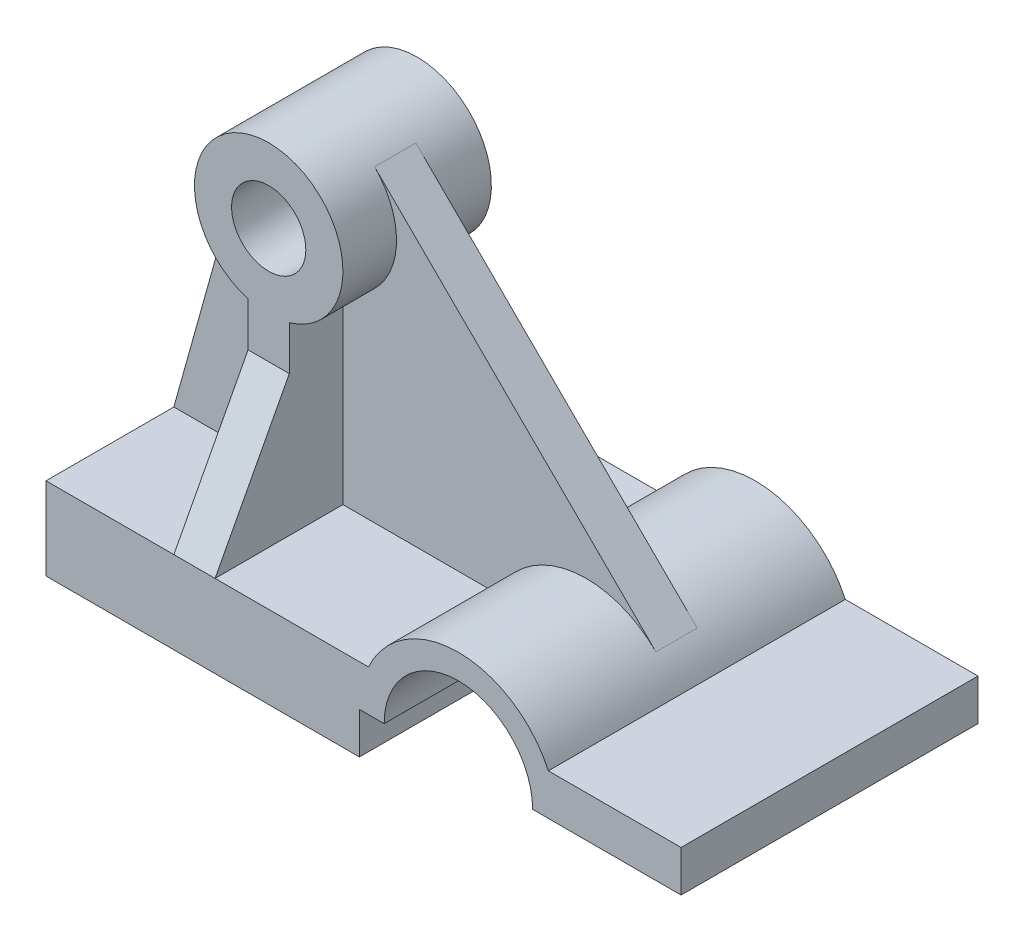
SolidWorks part; units mm, degrees
ref_plane "Front Plane" through (0, 0, 0) normal (0, 0, 1) x (1, 0, 0)
ref_plane "Top Plane" through (0, 0, 0) normal (0, 1, 0) x (1, 0, 0)
ref_plane "Right Plane" through (0, 0, 0) normal (1, 0, 0) x (0, 0, -1)
sketch "Sketch1" plane through (0, 0, 0) normal (0, 0, 1) x (1, 0, 0)
  line L0 (-41.1897, -1.8135) -> (34.8103, -1.8135)
  line L1 (34.8103, -1.8135) -> (34.8103, 8.1865)
  line L2 (34.8103, 8.1865) -> (40.8103, 8.1865)
  line L3 (76.8103, 8.1865) -> (112.8103, 8.1865)
  line L5 (112.8103, 18.1865) -> (80.6277, 18.1865)
  line L6 (36.9929, 18.1865) -> (-41.1897, 18.1865)
  line L7 (-41.1897, 18.1865) -> (-41.1897, -1.8135)
  line L8 (112.8103, 8.1865) -> (112.8103, 18.1865)
  arc A0 (40.8103, 8.1865) -> (76.8103, 8.1865) centre (58.8103, 8.1865) cw
  arc A2 (80.6277, 18.1865) -> (36.9929, 18.1865) centre (58.8103, 8.1865) ccw
  dimension "D3" = 48
  dimension "D6" = 18
  dimension "D1" = 76
  dimension "D2" = 20
  dimension "D4" = 6
  dimension "D5" = 10
  dimension "D7" = 54
extrude "Boss-Extrude1" add sketch "Sketch1" against normal blind 72
sketch "Sketch2" plane through (0, 18.1865, 0) normal (0, 1, 0) x (1, 0, 0)
  line L0 (-41.1897, 72) -> (-41.1897, 0) construction
  line L1 (-23.1897, 54) -> (12.8103, 54)
  line L2 (-23.1897, 54) -> (-23.1897, 18)
  line L3 (-23.1897, 18) -> (12.8103, 18)
  line L4 (12.8103, 54) -> (12.8103, 18)
  line L5 (-23.1897, 54) -> (12.8103, 18) construction
  line L6 (-23.1897, 18) -> (12.8103, 54) construction
  line L8 (36.9929, 0) -> (-41.1897, 0) construction
  point P0 (-5.1897, 36)
  point P9 (-13.1546, 0)
  point P10 (-31.1416, 34.8758)
  dimension "D1" = 36
  dimension "D2" = 36
  dimension "D3" = 36
  dimension "D4" = 36
extrude "Boss-Extrude3" add sketch "Sketch2" along normal blind 80
sketch "Sketch4" plane through (0, 0, -18) normal (0, 0, 1) x (1, 0, 0)
  line L0 (-23.1897, 18.1865) -> (12.8103, 18.1865) construction
  line L1 (12.8103, 98.1865) -> (12.8103, 18.1865) construction
  line L2 (-23.1897, 80.1865) -> (-23.1897, 98.1865)
  line L3 (-23.1897, 98.1865) -> (12.8103, 98.1865)
  line L4 (12.8103, 98.1865) -> (12.8103, 80.1865)
  line L5 (12.8103, 98.1865) -> (12.8103, 80.1865)
  circle A0 centre (-5.1897, 80.1865) radius 18
  circle A1 centre (-5.1897, 80.1865) radius 9
  dimension "D2" = 36
  dimension "D3" = 18
  dimension "D1" = 62
  dimension "D4" = 18
extrude "Cut-Extrude2" cut sketch "Sketch4" against normal blind 80 contours A1
sketch "Sketch5" plane through (0, 0, -18) normal (0, 0, 1) x (1, 0, 0)
  line L0 (-5.1897, 62.1865) -> (-5.1897, 18.1865) construction
  line L1 (-23.1897, 18.1865) -> (12.8103, 18.1865) construction
  line L2 (-10.1897, 62.1865) -> (-10.1897, 18.1865)
  line L3 (-0.1897, 62.1865) -> (-0.1897, 18.1865)
  line L4 (-10.1897, 18.1865) -> (-0.1897, 18.1865)
  line L5 (-23.1897, 80.1865) -> (-23.1897, 98.1865)
  line L6 (-23.1897, 98.1865) -> (12.8103, 98.1865)
  line L7 (12.8103, 98.1865) -> (12.8103, 80.1865)
  line L8 (12.8103, 80.1865) -> (12.8103, 18.1865)
  line L9 (12.8103, 18.1865) -> (-0.1897, 18.1865)
  line L10 (-0.1897, 18.1865) -> (34.811, 15.8347)
  line L11 (-23.1897, 80.1865) -> (-23.1897, 18.1865)
  line L12 (-23.1897, 18.1865) -> (-10.1897, 18.1865)
  line L13 (-0.1897, 62.1865) -> (-0.1897, 62.8949)
  line L14 (-10.1897, 62.1865) -> (-10.1897, 62.8949)
  circle A0 centre (-5.1897, 80.1865) radius 18
  line M3 (-23.1897, 18.1865) -> (12.8103, 18.1865)
  line M4 (12.8103, 18.1865) -> (12.8103, 98.1865)
  line M5 (12.8103, 98.1865) -> (-23.1897, 98.1865)
  line M6 (-23.1897, 98.1865) -> (-23.1897, 18.1865)
  dimension "D1" = 36
  dimension "D2" = 5
  dimension "D3" = 5
extrude "Cut-Extrude3" cut sketch "Sketch5" against normal blind 80 contours A0 L2 L14 M6 M3 | A0 L13 L3 M3 M4 | A0 M4 M5 | A0 L6 M6
ref_plane "Plane1" through (0, 0, -36) normal (0, 0, 1) x (1, 0, 0)
sketch "Sketch7" plane through (0, 0, -36) normal (0, 0, 1) x (1, 0, 0)
  line L0 (7.4927, 92.9598) -> (75.7202, 25.2175)
  arc A0 (-0.1897, 62.8949) -> (-10.1897, 62.8949) centre (-5.1897, 80.1865) ccw construction
  arc A1 (80.6277, 18.1865) -> (36.9929, 18.1865) centre (58.8103, 8.1865) ccw construction
rib "Rib1" sketch "Sketch7" sketch "Sketch7" thickness 10 extrusion direction parallel to sketch draft on no parameters "D1"=10
sketch "Sketch8" plane through (0, 0, -36) normal (0, 0, 1) x (1, 0, 0)
  line L0 (-22.5266, 85.0273) -> (-41.1897, 18.1865)
  arc A0 (-0.1897, 62.8949) -> (-10.1897, 62.8949) centre (-5.1897, 80.1865) ccw construction
rib "Rib4" sketch "Sketch8" sketch "Sketch8" thickness 10 extrusion direction parallel to sketch draft on no parameters "D1"=10
ref_plane "Plane4" through (-5.1897, 0, 0) normal (-1, 0, 0) x (0, 0, 1)
sketch "Sketch12" plane through (-5.1897, 0, 0) normal (-1, 0, 0) x (0, 0, 1)
  line L0 (-18, 52.1865) -> (0, 18.1865)
  line L1 (-18, 62.8949) -> (-18, 18.1865) construction
  dimension "D1" = 46
rib "Rib5" sketch "Sketch12" sketch "Sketch12" thickness 10 extrusion direction parallel to sketch draft on no parameters "D1"=10
